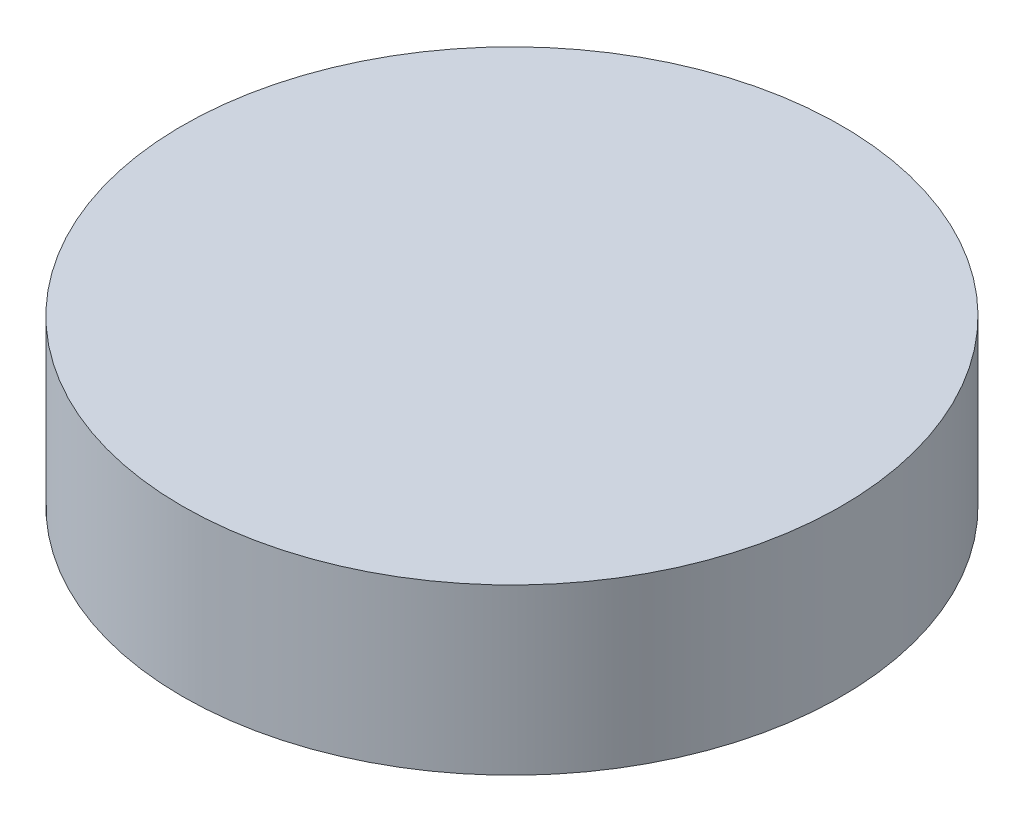
SolidWorks part; units mm, degrees
ref_plane "Front Plane" through (0, 0, 0) normal (0, 0, 1) x (1, 0, 0)
ref_plane "Top Plane" through (0, 0, 0) normal (0, 1, 0) x (1, 0, 0)
ref_plane "Right Plane" through (0, 0, 0) normal (1, 0, 0) x (0, 0, -1)
sketch "Sketch1" plane through (0, 0, 0) normal (0, 1, 0) x (1, 0, 0)
  circle A0 centre (0, 0) radius 2.54
  dimension "D1" = 5.08
extrude "Boss-Extrude1" add sketch "Sketch1" along normal blind 1.27
